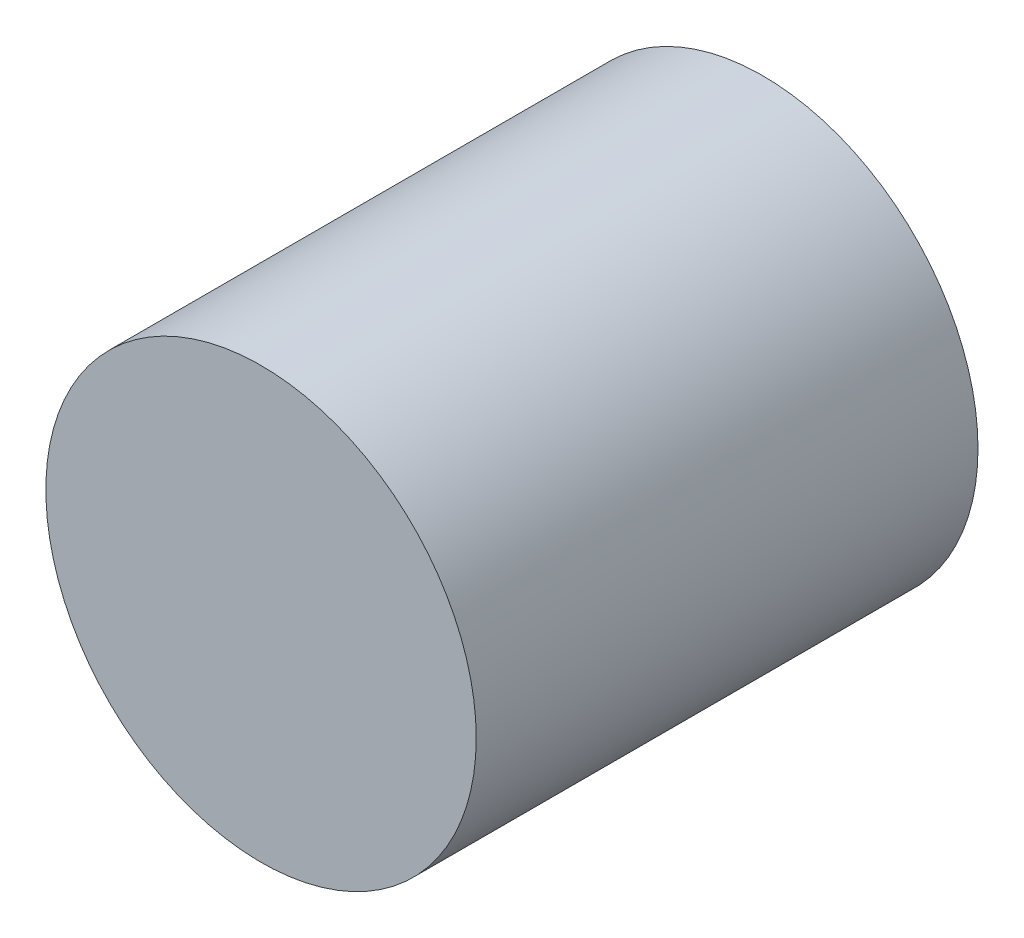
SolidWorks part; units mm, degrees
material "1023 Carbon Steel Sheet (SS)"
ref_plane "Front Plane" through (0, 0, 0) normal (0, 0, 1) x (1, 0, 0)
ref_plane "Top Plane" through (0, 0, 0) normal (0, 1, 0) x (1, 0, 0)
ref_plane "Right Plane" through (0, 0, 0) normal (1, 0, 0) x (0, 0, -1)
sketch "Sketch1" plane through (0, 0, 0) normal (0, 0, 1) x (1, 0, 0)
  circle A0 centre (0, 0) radius 6.35
extrude "Boss-Extrude1" add sketch "Sketch1" along normal blind 14.8061
